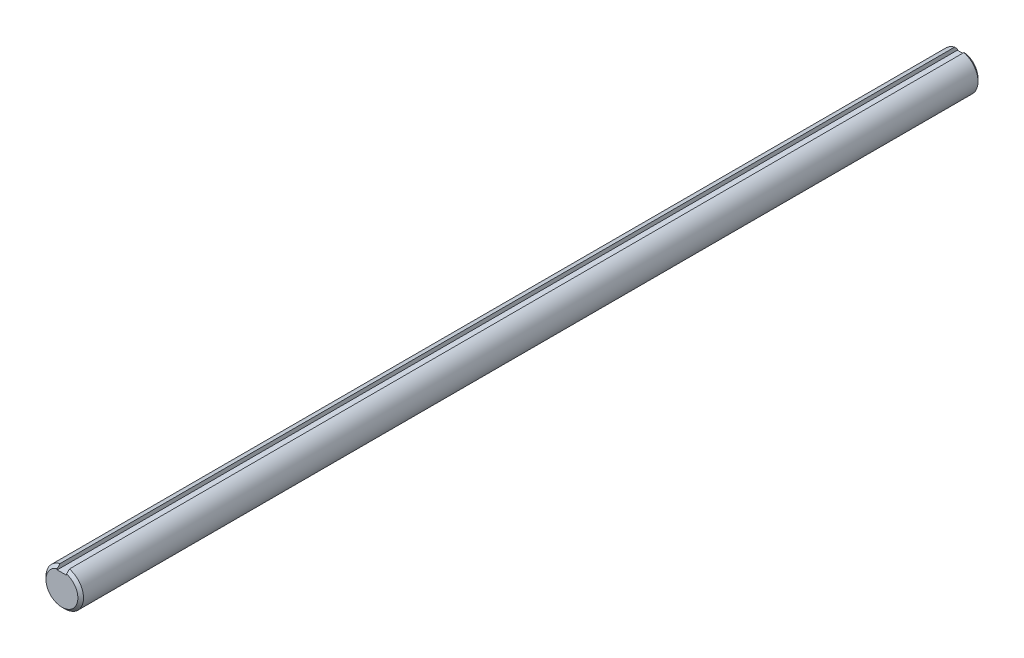
SolidWorks part; units mm, degrees
ref_plane "Front" through (0, 0, 0) normal (0, 0, 1) x (1, 0, 0)
ref_plane "Top" through (0, 0, 0) normal (0, 1, 0) x (1, 0, 0)
ref_plane "Right" through (0, 0, 0) normal (1, 0, 0) x (0, 0, -1)
sketch "Sketch1" plane through (0, 0, 0) normal (0, 0, 1) x (1, 0, 0)
  circle A0 centre (0, 0) radius 6.35
  dimension "dia" = 12.7
extrude "Extrude1" add sketch "Sketch1" along normal mid plane 304.8
sketch "Sketch2" plane through (0, 0, 0) normal (1, 0, 0) x (0, 0, -1)
  point P0 (-152.4, 6.35)
  point P1 (152.4, 6.35)
  point P2 (152.4, -6.35)
chamfer "Chamfer1" distance 0.9525 angle 45 2 edges at (6.35, 0, -152.4) (6.35, 0, 152.4)
sketch "Sketch3" plane through (0, 0, 0) normal (0, 0, 1) x (1, 0, 0)
  line L1 (-1.5875, 6.35) -> (1.5875, 6.35)
  line L2 (-1.5875, 6.35) -> (-1.5875, 4.7625)
  line L3 (-1.5875, 4.7625) -> (1.5875, 4.7625)
  line L4 (1.5875, 6.35) -> (1.5875, 4.7625)
  dimension "key wd" = 3.175
  dimension "key dp" = 1.5875
extrude "Extrude2" cut sketch "Sketch3" against normal through all and the other way through all
equation "\"D1@Chamfer1\" = \"dia@Sketch1\" * .075"
